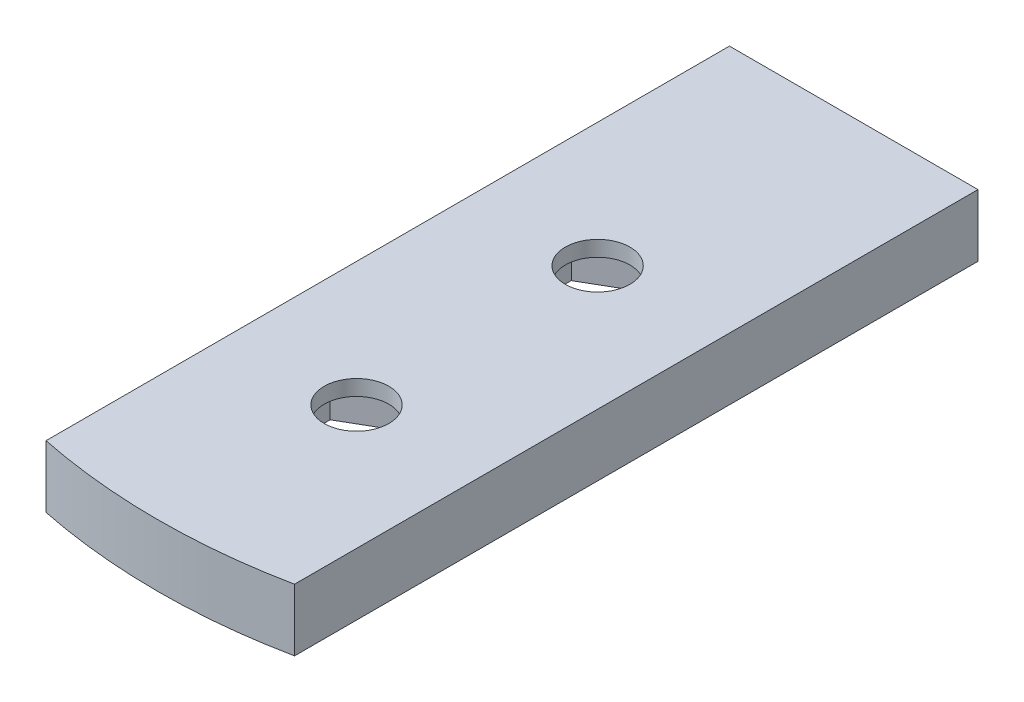
SolidWorks part; units mm, degrees
ref_plane "Front Plane" through (0, 0, 0) normal (0, 0, 1) x (1, 0, 0)
ref_plane "Top Plane" through (0, 0, 0) normal (0, 1, 0) x (1, 0, 0)
ref_plane "Right Plane" through (0, 0, 0) normal (1, 0, 0) x (0, 0, -1)
sketch "Sketch1" plane through (0, 0, 0) normal (0, 1, 0) x (1, 0, 0)
  line L1 (-6.3558, -10.1273) -> (6.3442, -10.1273)
  line L2 (-6.3558, -10.1273) -> (-6.3558, -45.0523)
  line L4 (6.3442, -10.1273) -> (6.3442, -45.0523)
  line L5 (3.1819, -25.0552) -> (3.1819, -21.3743)
  line L6 (3.1819, -21.3743) -> (-0.0058, -19.5339)
  line L7 (-0.0058, -19.5339) -> (-3.1935, -21.3743)
  line L8 (-3.1935, -21.3743) -> (-3.1935, -25.0552)
  line L9 (-3.1935, -25.0552) -> (-0.0058, -26.8956)
  line L10 (-0.0058, -26.8956) -> (3.1819, -25.0552)
  line L11 (3.1819, -37.3742) -> (3.1819, -33.6933)
  line L12 (3.1819, -33.6933) -> (-0.0058, -31.8529)
  line L13 (-0.0058, -31.8529) -> (-3.1935, -33.6933)
  line L14 (-3.1935, -33.6933) -> (-3.1935, -37.3742)
  line L15 (-3.1935, -37.3742) -> (-0.0058, -39.2146)
  line L16 (-0.0058, -39.2146) -> (3.1819, -37.3742)
  circle A0 centre (-0.0058, -23.2148) radius 3.1877 construction
  circle A1 centre (-0.0058, -35.5338) radius 3.1877 construction
  arc A4 (-6.3558, -45.0523) -> (6.3442, -45.0523) centre (-0.0058, -13.9438) ccw
  circle A5 centre (-0.0058, -35.5338) radius 1.651 construction
  circle A6 centre (-0.0058, -23.2148) radius 1.651 construction
  circle A7 centre (-0.0058, -13.9438) radius 31.75 construction
  point P26 (-0.0058, -10.1273)
  dimension "D1" = 6.3754
  dimension "D2" = 34.925
  dimension "D3" = 12.7
extrude "Boss-Extrude1" add sketch "Sketch1" along normal blind 2.3813
sketch "Sketch2" plane through (0, 2.3813, 0) normal (0, 1, 0) x (1, 0, 0)
  line L0 (6.3442, -45.0523) -> (6.3442, -10.1273) construction
  line L1 (-6.3558, -10.1273) -> (-6.3558, -45.0523) construction
  line L2 (6.3442, -10.1273) -> (-6.3558, -10.1273) construction
  line L3 (6.3442, -45.0523) -> (6.3442, -10.1273)
  line L4 (-6.3558, -10.1273) -> (-6.3558, -45.0523)
  line L5 (6.3442, -10.1273) -> (-6.3558, -10.1273)
  arc A0 (-6.3558, -45.0523) -> (6.3442, -45.0523) centre (-0.0058, -13.9438) ccw construction
  arc A1 (-6.3558, -45.0523) -> (6.3442, -45.0523) centre (-0.0058, -13.9438) ccw
  circle A2 centre (-0.0058, -23.2148) radius 1.651
  circle A3 centre (-0.0058, -35.5338) radius 1.651
extrude "Boss-Extrude2" add sketch "Sketch2" along normal blind 0.7937
